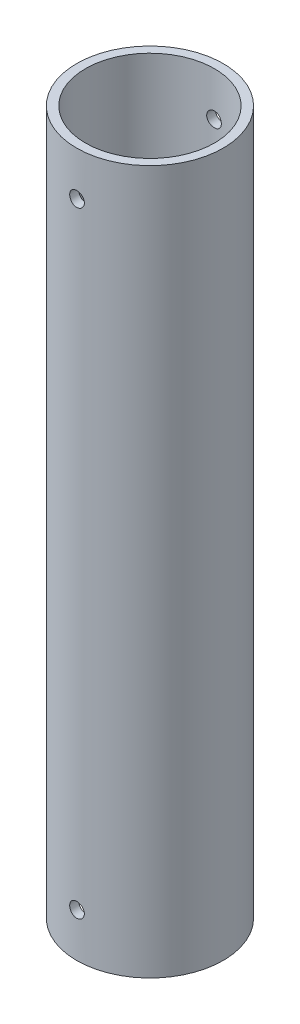
SolidWorks part; units mm, degrees
material "PVC Rígido"
ref_plane "Plano frontal" through (0, 0, 0) normal (0, 0, 1) x (1, 0, 0)
ref_plane "Plano superior" through (0, 0, 0) normal (0, 1, 0) x (1, 0, 0)
ref_plane "Plano direito" through (0, 0, 0) normal (1, 0, 0) x (0, 0, -1)
sketch "Esboço1" plane through (0, 0, 0) normal (0, 1, 0) x (1, 0, 0)
  circle A0 centre (0, 0) radius 22
  circle A1 centre (0, 0) radius 25
  dimension "D1" = 44
  dimension "D2" = 50
extrude "Ressalto-extrusão1" add sketch "Esboço1" along normal blind 240
sketch "Esboço2" plane through (0, 0, 0) normal (0, 0, 1) x (1, 0, 0)
  circle A0 centre (0, 15) radius 2.5
  dimension "D1" = 5
  dimension "D2" = 15
extrude "Corte-extrusão1" cut sketch "Esboço2" against normal through all both and the other way through all
sketch "Esboço3" plane through (0, 0, 0) normal (1, 0, 0) x (0, 0, -1)
  circle A0 centre (0, 15) radius 2.5
  dimension "D2" = 5
  dimension "D1" = 15
extrude "Corte-extrusão2" [suppressed] cut sketch "Esboço3" against normal through all both and the other way through all
ref_plane "Plano1" through (0, 120, 0) normal (0, -1, 0) x (-1, 0, 0)
mirror "Espelhar1" about plane through (0, 120, 0) normal (0, -1, 0) of "Corte-extrusão1", "Corte-extrusão2"
